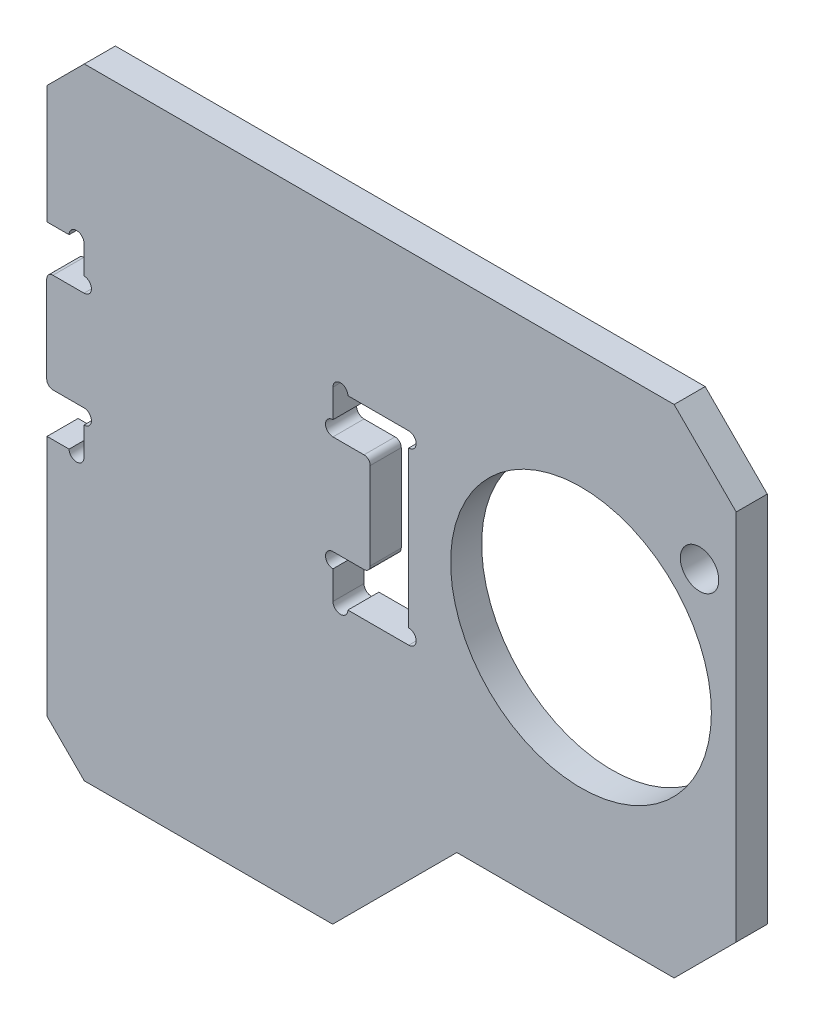
SolidWorks part; units mm, degrees
ref_plane "前视基准面" through (0, 0, 0) normal (0, 0, 1) x (1, 0, 0)
ref_plane "上视基准面" through (0, 0, 0) normal (0, 1, 0) x (1, 0, 0)
ref_plane "右视基准面" through (0, 0, 0) normal (1, 0, 0) x (0, 0, -1)
sketch "草图1" plane through (0, 0, 0) normal (0, 0, 1) x (1, 0, 0)
  line L0 (-13, 20) -> (-13, 7.475)
  line L1 (-13, 7.475) -> (-10.025, 7.475)
  line L2 (-10.025, 7.475) -> (-10.025, 4)
  line L3 (-10.025, -7.475) -> (-13, -7.475)
  line L4 (-13, -7.475) -> (-13, -30)
  line L5 (-13, -30) -> (42.5, -30)
  line L6 (42.5, -30) -> (42.5, 20)
  line L7 (42.5, 20) -> (-13, 20)
  line L8 (-13.025, 0) -> (0, 0) construction
  line L9 (-10.025, 4) -> (-13.025, 4)
  line L10 (-13.025, 4) -> (-13.025, -4)
  line L11 (-13.025, -4) -> (-10.025, -4)
  line L12 (-10.025, -4) -> (-10.025, -7.475)
  line L13 (10.025, 7.475) -> (10.025, 4)
  line L14 (10.025, 4) -> (13.025, 4)
  line L15 (13.025, 4) -> (13.025, -4)
  line L16 (13.025, -4) -> (10.025, -4)
  line L17 (10.025, -4) -> (10.025, -7.475)
  line L18 (10.025, -7.475) -> (16.125, -7.475)
  line L19 (16.125, -7.475) -> (16.125, 7.475)
  line L20 (16.125, 7.475) -> (10.025, 7.475)
  line L21 (0, 7.475) -> (0, -7.475) construction
  line L22 (-10.025, 7.475) -> (10.025, 7.475) construction
  point P4 (-13.025, 0)
  point P26 (-5.6748, 9.7075)
  point P27 (0, 0)
  point P28 (16.125, 9.8557)
  dimension "D1" = 3
  dimension "D2" = 13
  dimension "D3" = 20.05
  dimension "D4" = 8
  dimension "D5" = 14.95
  dimension "D6" = 3.1
  dimension "D7" = 55.5
  dimension "D8" = 20
  dimension "D9" = 30
extrude "凸台-拉伸1" add sketch "草图1" along normal mid plane 2.5
sketch "草图2" plane through (0, 0, 1.25) normal (0, 0, 1) x (1, 0, 0)
  line L0 (16.125, 7.475) -> (10.025, 7.475) construction
  line L1 (16.125, -7.475) -> (16.125, 7.475) construction
  line L2 (10.025, 7.475) -> (10.025, 4) construction
  line L3 (10.025, -4) -> (10.025, -7.475) construction
  line L4 (10.025, -7.475) -> (16.125, -7.475) construction
  line L6 (-10.025, -7.475) -> (-13, -7.475) construction
  line L7 (-13, 7.475) -> (-10.025, 7.475) construction
  line L8 (-10.025, 7.475) -> (-10.025, 4) construction
  line L9 (-10.025, -4) -> (-10.025, -7.475) construction
  circle A0 centre (10.625, 7.475) radius 0.6
  circle A1 centre (16.125, 6.875) radius 0.6
  circle A2 centre (10.025, 4.6) radius 0.6
  circle A3 centre (10.025, -4.6) radius 0.6
  circle A4 centre (10.625, -7.475) radius 0.6
  circle A5 centre (16.125, -6.875) radius 0.6
  circle A6 centre (-10.025, -4.6) radius 0.6
  circle A7 centre (-10.625, -7.475) radius 0.6
  circle A8 centre (-10.625, 7.475) radius 0.6
  circle A9 centre (-10.025, 4.6) radius 0.6
  point P30 (-10.025, -4.4236)
  point P47 (-10.025, -5.75)
  dimension "D1" = 1.2
extrude "切除-拉伸1" cut sketch "草图2" against normal through all
fillet "圆角1" radius 0.5 4 edges at (13.025, -4, 0) (13.025, 4, 0) (-13.025, -4, 0) (-13.025, 4, 0)
sketch "草图3" plane through (0, 0, 1.25) normal (0, 0, 1) x (1, 0, 0)
  line L0 (-13, 20) -> (-13, 7.475) construction
  circle A0 centre (30, 0) radius 10.5
  point P2 (0, 0)
  point P4 (0, 0)
  point P5 (30.0389, 0)
  dimension "D1" = 21
  dimension "D2" = 43
extrude "切除-拉伸2" cut sketch "草图3" against normal through all
chamfer "倒角1" distance 5 angle 45 1 edges at (42.5, 20, 0)
chamfer "倒角2" distance 15 angle 45 1 edges at (42.5, -30, 0)
chamfer "倒角3" distance 3 angle 45 2 edges at (-13, -30, 0) (-13, 20, 0)
sketch "草图5" plane through (0, 0, -1.25) normal (0, 0, -1) x (-1, 0, 0)
  line L0 (-37.5, -20) -> (-20, -20)
  line L1 (-42.5, -15) -> (-27.5, -30) construction
  line L2 (-20, -20) -> (-10, -30)
  line L3 (10, -30) -> (-27.5, -30) construction
  line L4 (-37.5, -20) -> (-27.5, -30)
  line L5 (-27.5, -30) -> (-10, -30)
  line L6 (-42.5, -15) -> (-42.5, 15) construction
  dimension "D1" = 5
  dimension "D2" = 32.5
extrude "切除-拉伸4" cut sketch "草图5" against normal through all
sketch "草图6" plane through (0, 0, -1.25) normal (0, 0, -1) x (-1, 0, 0)
  line L0 (-39.5459, 9.5459) -> (-30, 0) construction
  line L1 (-30, 0) -> (-30, 13.5) construction
  circle A0 centre (-30, 0) radius 13.5 construction
  circle A1 centre (-39.5459, 9.5459) radius 3 construction
  circle A4 centre (-30, 0) radius 10.5 construction
  circle A5 centre (-39.5459, 9.5459) radius 1.55
  dimension "D1" = 6
  dimension "D3" = 3.1
  dimension "D2" = 45
extrude "切除-拉伸5" cut sketch "草图6" against normal through all
